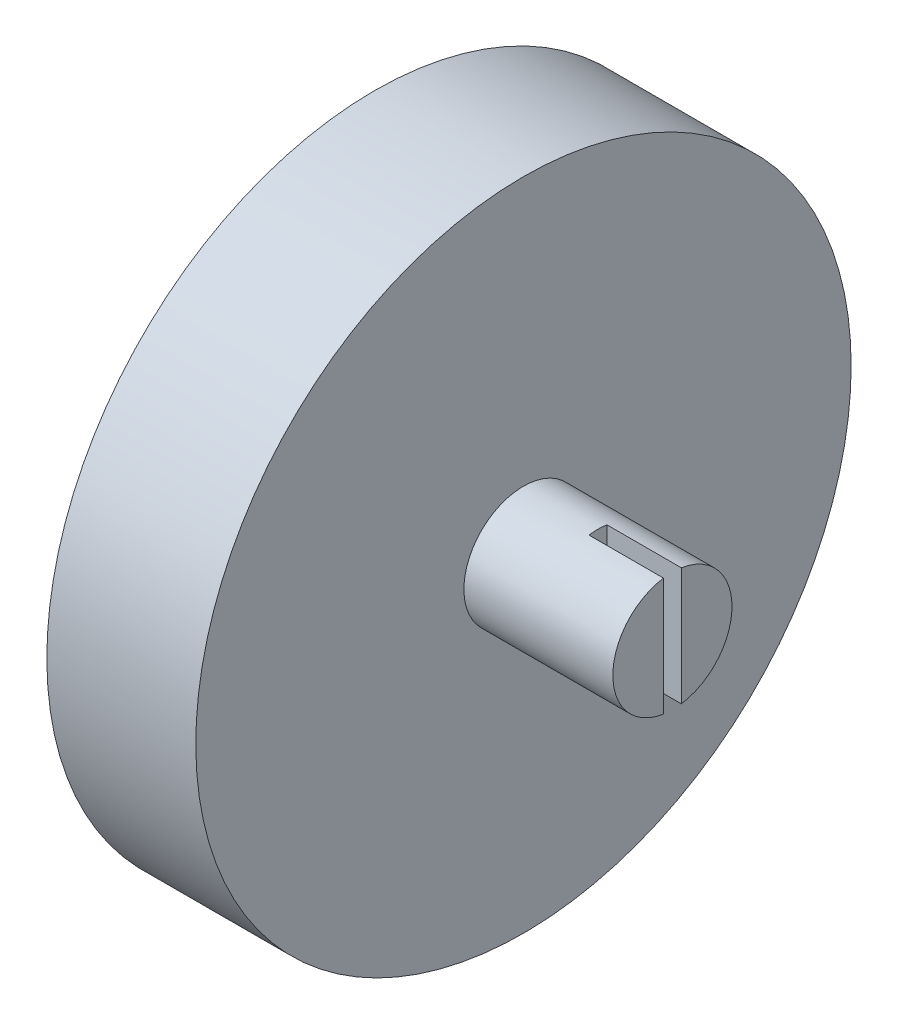
SolidWorks part; units mm, degrees
ref_plane "Front Plane" through (0, 0, 0) normal (0, 0, 1) x (1, 0, 0)
ref_plane "Top Plane" through (0, 0, 0) normal (0, 1, 0) x (1, 0, 0)
ref_plane "Right Plane" through (0, 0, 0) normal (1, 0, 0) x (0, 0, -1)
sketch "Sketch1" plane through (0, 0, 0) normal (1, 0, 0) x (0, 0, -1)
  circle A0 centre (0, 0) radius 22
  dimension "D1" = 44
extrude "Boss-Extrude1" add sketch "Sketch1" along normal blind 10
sketch "Sketch8" plane through (0, 0, 0) normal (1, 0, 0) x (0, 0, -1)
  line L0 (-0.6, -5) -> (0.6, 5) construction
  line L1 (-0.6, 5) -> (0.6, -5) construction
  line L2 (-0.6, -5) -> (0.6, -5)
  line L3 (-0.6, 5) -> (0.6, 5)
  line L4 (-0.6, 5) -> (-0.6, -5)
  line L5 (0.6, -5) -> (0.6, 5)
  point P4 (0, 0)
  dimension "D1" = 1.2
  dimension "D2" = 10
sketch "Sketch13" plane through (0, 0, 0) normal (1, 0, 0) x (0, 0, -1)
  line L0 (-2.6704, -16.8582) -> (-2.6704, -16.5304)
  line L1 (6.5, 19.5569) -> (6.5, -6.9431)
  line L2 (-6.5, 19.5569) -> (-6.5, -6.9431)
  line L3 (0, -25.25) -> (0, 0) construction
  line L4 (2.6704, -16.8582) -> (2.6704, -16.5304)
  line L5 (-4.7624, -10) -> (-2.6704, -16.5304)
  line L6 (0, -25.25) -> (-1.0006, -21.9772)
  line L7 (-6.5, 19.5569) -> (6.5, 19.5569)
  line L8 (-6.5, -6.9431) -> (-4.7624, -6.9431)
  line L9 (6.5, -6.9431) -> (4.7624, -6.9431)
  line L10 (1.0006, -21.9772) -> (0, -25.25)
  line L11 (4.7624, -10) -> (2.6704, -16.5304)
  line L12 (-2.6704, -16.8582) -> (-2.6704, -21.8373)
  line L13 (-4.7624, -10) -> (-4.7624, -6.9431)
  line L14 (4.7624, -10) -> (4.7624, -6.9431)
  line L15 (2.6704, -16.8582) -> (2.6704, -21.8373)
  arc A0 (-2.6704, -21.8373) -> (-1.0006, -21.9772) centre (0, 0) ccw
  arc A1 (1.0006, -21.9772) -> (2.6704, -21.8373) centre (0, 0) ccw
  dimension "D1" = 13
  dimension "D2" = 26.5
  dimension "D3" = 3.0569
  dimension "D4" = 25.25
extrude "Cut-Extrude2" cut sketch "Sketch13" along normal blind 5.5 contours L1 L9 L14 L11 L4 L15 A1 L10 L6 A0 L12 L0 L5 L13 L8 L2 L7
sketch "Sketch15" plane through (0, 0, 0) normal (-1, 0, 0) x (0, 0, 1)
  line L0 (9, 17.1749) -> (9, -6.9431)
  line L1 (9, 17.1749) -> (-9, 17.1749)
  line L2 (9, -6.9431) -> (-9, -6.9431)
  line L3 (0, -6.9431) -> (0, 17.1749) construction
  line L4 (-9, -6.9431) -> (-9, 17.1749)
  line L5 (-6.5, -6.9431) -> (-4.7624, -6.9431) construction
  point P4 (0, -6.9431)
  point P7 (0, 17.1749)
  dimension "D1" = 18
  dimension "D2" = 24.118
extrude "Cut-Extrude3" cut sketch "Sketch15" against normal blind 3
sketch "Sketch16" plane through (10, 0, 0) normal (1, 0, 0) x (0, 0, -1)
  circle A0 centre (0, 0) radius 4
  dimension "D1" = 8
extrude "Boss-Extrude2" add sketch "Sketch16" along normal blind 10
extrude "Cut-Extrude4" cut sketch "Sketch8" against normal blind 5 from offset 20
sketch "Sketch17" plane through (0, -6.9431, 0) normal (0, 1, 0) x (1, 0, 0)
  line L0 (0, 4.7624) -> (0, 6.5124)
  line L1 (0, 9) -> (0, 4.7624) construction
  line L2 (0, 6.5124) -> (4, 6.5124)
  line L3 (4, 6.5124) -> (4, 4.7624)
  line L4 (5.5, 4.7624) -> (0, 4.7624) construction
  line L5 (4, 4.7624) -> (0, 4.7624)
  dimension "D1" = 1.75
  dimension "D2" = 4
extrude "Boss-Extrude3" add sketch "Sketch17" along normal blind 1
sketch "Sketch18" plane through (0, -6.9431, 0) normal (0, 1, 0) x (1, 0, 0)
  line L0 (5.5, -6.5) -> (3, -6.5) construction
  line L1 (0, -4.7624) -> (4.25, -4.7624)
  line L2 (0, -4.7624) -> (0, -6.5)
  line L3 (0, -6.5) -> (4.25, -6.5)
  line L4 (4.25, -4.7624) -> (4.25, -6.5)
  dimension "D1" = 1.7376
extrude "Boss-Extrude4" add sketch "Sketch18" along normal blind 1
sketch "Sketch22" plane through (0, 0, 0) normal (1, 0, 0) x (0, 0, -1)
  line L0 (0, 0) -> (0, 16.8191) construction
  circle A0 centre (-14, 0) radius 1.5
  circle A1 centre (14, 0) radius 1.5
  dimension "D1" = 3
  dimension "D2" = 14
extrude "Cut-Extrude7" cut sketch "Sketch22" along normal blind 7 from surface at 0 starting at face at (0, 0.1685, -0.0012)
